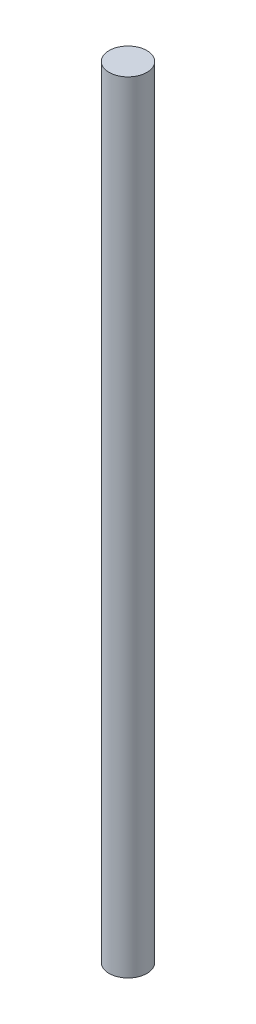
SolidWorks part; units mm, degrees
ref_plane "Front Plane" through (0, 0, 0) normal (0, 0, 1) x (1, 0, 0)
ref_plane "Top Plane" through (0, 0, 0) normal (0, 1, 0) x (1, 0, 0)
ref_plane "Right Plane" through (0, 0, 0) normal (1, 0, 0) x (0, 0, -1)
sketch "Sketch1" plane through (0, 0, 0) normal (0, 1, 0) x (1, 0, 0)
  circle A0 centre (0, 0) radius 4
  dimension "D1" = 8
extrude "Boss-Extrude1" add sketch "Sketch1" along normal blind 165
